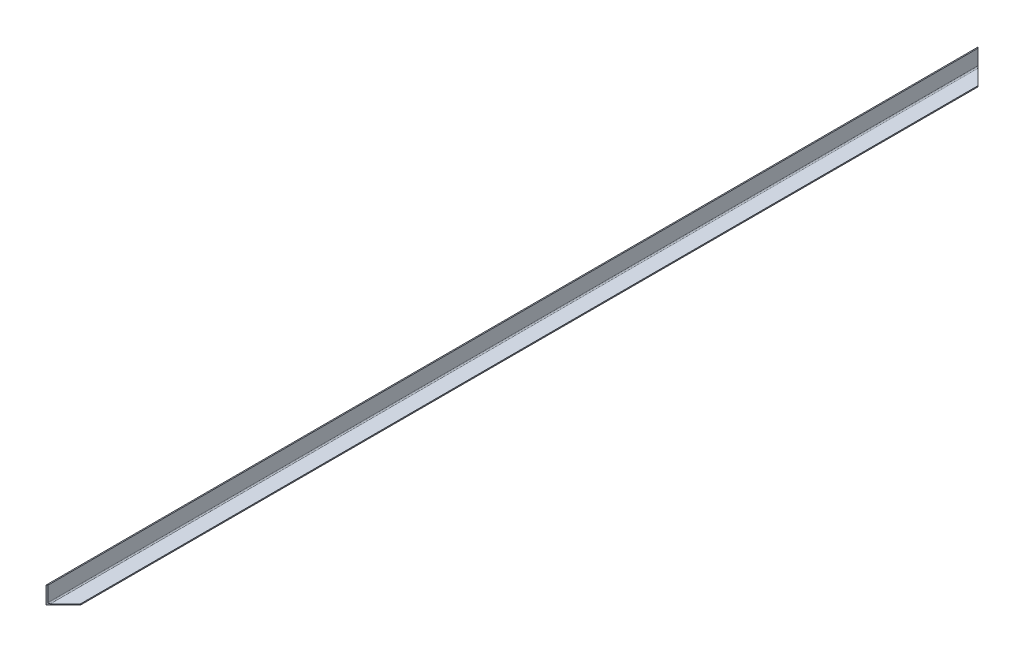
SolidWorks part; units mm, degrees
ref_plane "Front Plane" through (0, 0, 0) normal (0, 0, 1) x (1, 0, 0)
ref_plane "Top Plane" through (0, 0, 0) normal (0, 1, 0) x (1, 0, 0)
ref_plane "Right Plane" through (0, 0, 0) normal (1, 0, 0) x (0, 0, -1)
sketch "Sketch1" plane through (0, 0, 0) normal (0, 0, 1) x (1, 0, 0)
  line L0 (0, -25.4) -> (0, 25.4) construction
  line L1 (25.4, 0) -> (-25.4, 0) construction
  line L2 (-25.4, 25.4) -> (-25.4, -25.4) construction
  line L3 (-25.4, -25.4) -> (25.4, -25.4) construction
  line L4 (25.4, -25.4) -> (25.4, -22.225) construction
  line L5 (25.4, -22.225) -> (-22.225, -22.225) construction
  line L6 (-22.225, -22.225) -> (-22.225, 25.4) construction
  line L7 (-22.225, 25.4) -> (-25.4, 25.4) construction
  line L8 (-22.225, -22.225) -> (-25.4, -22.225) construction
  line L9 (-22.225, -22.225) -> (-22.225, -25.4) construction
  point P4 (0, 0)
  point P8 (0, 0)
  dimension "Wall Thickness" = 3.175
  dimension "Outside Height" = 50.8
  dimension "Outside Width" = 50.8
  dimension "Inside Width" = 47.625
  dimension "Inside Height" = 47.625
sketch "Sketch2" plane through (0, 0, 0) normal (1, 0, 0) x (0, 0, -1)
  line L0 (1368.425, 0) -> (-1368.425, 0) construction
  line L1 (1368.425, -25.4) -> (-1368.425, -25.4) construction
  point P0 (-1304.925, 0)
  point P4 (0, 0)
  point P5 (1304.925, 0)
  point P9 (0, -25.4)
  dimension "Length" = 2736.85
  dimension "D1" = 63.5
  dimension "D2" = 63.5
sketch "Sketch4" plane through (0, 0, 0) normal (0, 0, 1) x (1, 0, 0)
  line L0 (-22.225, -22.225) -> (-22.225, 25.4) construction
  line L1 (25.4, -22.225) -> (-22.225, -22.225) construction
  line L2 (25.4, -25.4) -> (25.4, -22.225) construction
  line L3 (-25.4, -25.4) -> (25.4, -25.4) construction
  line L4 (-25.4, 25.4) -> (-25.4, -25.4) construction
  line L5 (-22.225, 25.4) -> (-25.4, 25.4) construction
  line L6 (-22.225, -18.8383) -> (-22.225, 25.4)
  line L7 (25.4, -22.225) -> (-18.8383, -22.225)
  line L8 (25.4, -25.4) -> (25.4, -22.225)
  line L9 (-25.4, -25.4) -> (25.4, -25.4)
  line L10 (-25.4, 25.4) -> (-25.4, -25.4)
  line L11 (-22.225, 25.4) -> (-25.4, 25.4)
  arc A0 (-22.225, -18.8383) -> (-18.8383, -22.225) centre (-18.8383, -18.8383) ccw
  dimension "D1" = 3.3867
extrude "Boss-Extrude1" add sketch "Sketch4" against normal up to vertex (1368.425 mm away) and the other way up to vertex (1368.425 mm away) up to point (0, 0, -1368.425) other way up to point (0, 0, 1368.425)
sketch "Sketch5" plane through (0, -22.225, 0) normal (0, 1, 0) x (1, 0, 0)
  line L0 (-25.4, 1368.425) -> (25.4, 1317.625)
  line L1 (25.4, 1368.425) -> (25.4, -1368.425) construction
  line L2 (25.4, 1317.625) -> (25.4, 1368.425)
  line L3 (25.4, 1368.425) -> (-25.4, 1368.425)
  line L4 (-27.94, 0) -> (27.94, 0) construction
  line L5 (25.4, -1368.425) -> (-25.4, -1368.425)
  line L6 (25.4, -1317.625) -> (25.4, -1368.425)
  line L7 (-25.4, -1368.425) -> (25.4, -1317.625)
  dimension "D1" = 50.8
extrude "Cut-Extrude1" cut sketch "Sketch5" against normal through all both and the other way through all
equation "\"D1@Sketch2\"=\"Outside Height@Sketch1\"*1.25"
equation "\"D2@Sketch2\"=\"D1@Sketch2\""
equation "\"D1@Sketch4\"=\"Outside Height@Sketch1\"/15"
